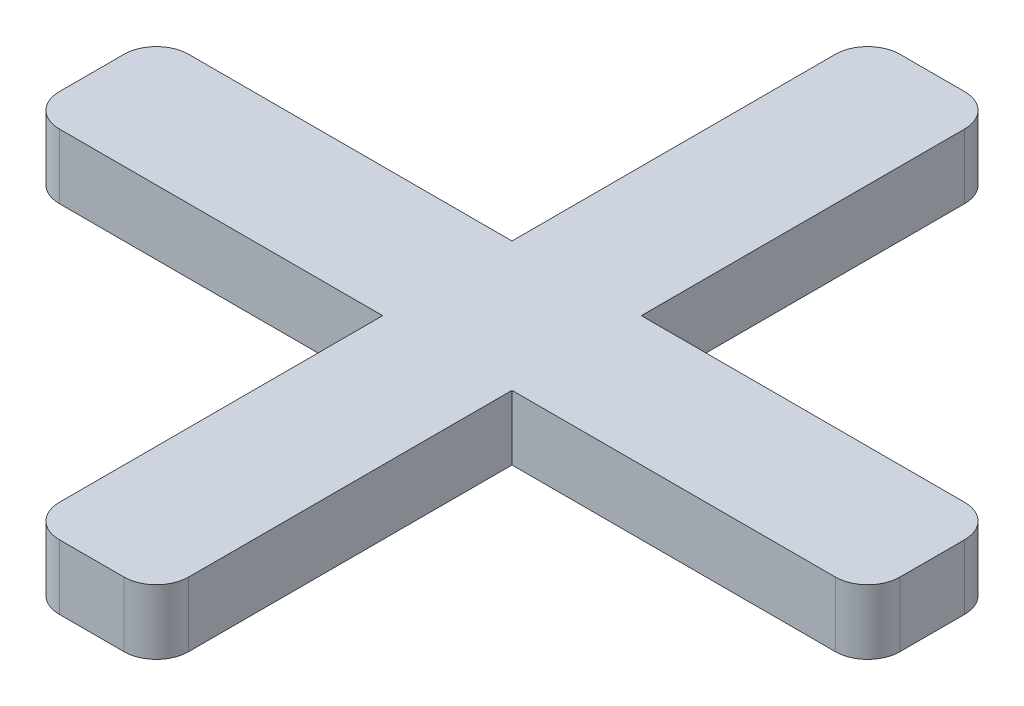
SolidWorks part; units mm, degrees
ref_plane "Front Plane" through (0, 0, 0) normal (0, 0, 1) x (1, 0, 0)
ref_plane "Top Plane" through (0, 0, 0) normal (0, 1, 0) x (1, 0, 0)
ref_plane "Right Plane" through (0, 0, 0) normal (1, 0, 0) x (0, 0, -1)
sketch "Sketch2" plane through (0, 0, 0) normal (0, 1, 0) x (1, 0, 0)
  line L1 (-6, 1) -> (-1, 1)
  line L2 (-6.5, 0.5) -> (-6.5, -0.5)
  line L3 (-6, -1) -> (-1, -1)
  line L4 (6.5, 0.5) -> (6.5, -0.5)
  line L5 (-6.5, 1) -> (-6.2074, 0.955) construction
  line L6 (-6.5, -1) -> (-6.2074, -0.955) construction
  line L7 (-0.5, -6.5) -> (0.5, -6.5)
  line L8 (-1, -6) -> (-1, -1)
  line L9 (-0.5, 6.5) -> (0.5, 6.5)
  line L10 (1, -6) -> (1, -1)
  line L11 (-1, -6.5) -> (-0.955, -6.2074) construction
  line L12 (-1, 6.5) -> (-0.955, 6.2074) construction
  line L14 (0.955, 6.2074) -> (1, 6.5) construction
  line L15 (1, 1) -> (6, 1)
  line L16 (6.2074, 0.955) -> (6.5, 1) construction
  line L17 (6.2074, -0.955) -> (6.5, -1) construction
  line L18 (0.955, -6.2074) -> (1, -6.5) construction
  line L20 (1, -1) -> (6, -1)
  line L21 (-1, 1) -> (-1, 6)
  line L22 (1, 1) -> (1, 6)
  arc A0 (-1, 6) -> (-0.5, 6.5) centre (-0.5, 6) cw
  arc A1 (0.5, 6.5) -> (1, 6) centre (0.5, 6) cw
  arc A2 (6, 1) -> (6.5, 0.5) centre (6, 0.5) cw
  arc A3 (6, -1) -> (6.5, -0.5) centre (6, -0.5) ccw
  arc A4 (0.5, -6.5) -> (1, -6) centre (0.5, -6) ccw
  arc A5 (-0.5, -6.5) -> (-1, -6) centre (-0.5, -6) cw
  arc A6 (-6.5, -0.5) -> (-6, -1) centre (-6, -0.5) ccw
  arc A7 (-6, 1) -> (-6.5, 0.5) centre (-6, 0.5) ccw
  point P0 (0, 0)
  point P6 (0, 0)
  dimension "D5" = 0.5
  dimension "D1" = 13
  dimension "D2" = 2
  dimension "D3" = 2
  dimension "D4" = 13
extrude "Boss-Extrude1" add sketch "Sketch2" along normal blind 1
